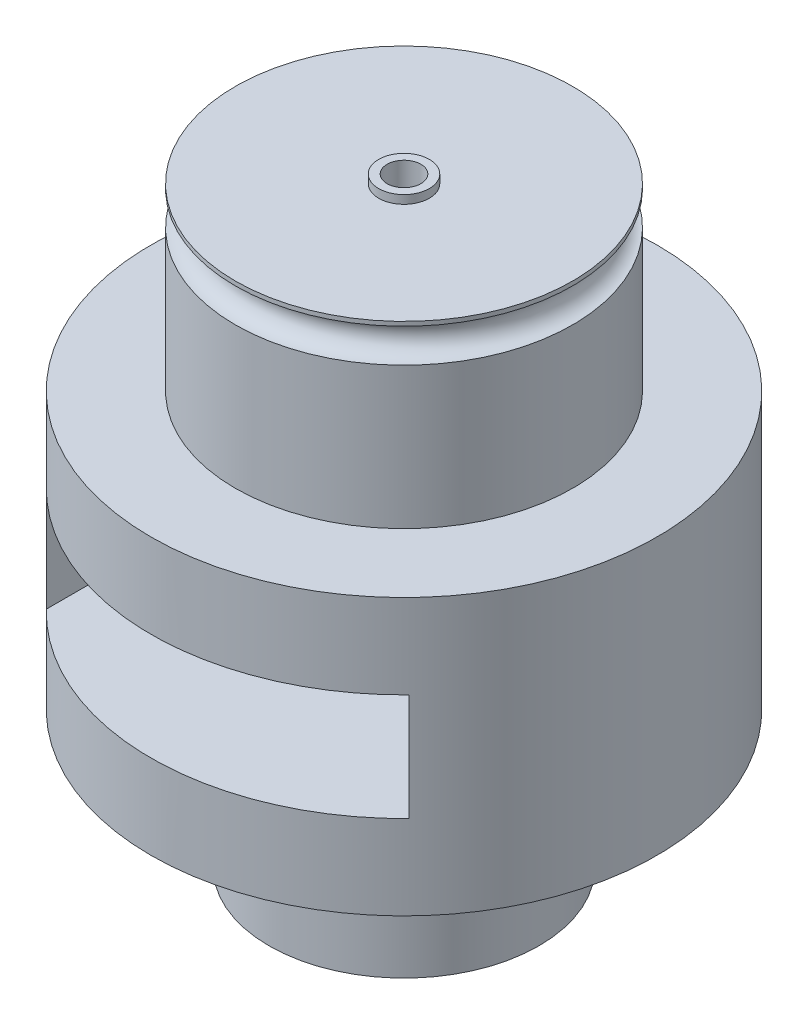
SolidWorks part; units mm, degrees
ref_plane "Front Plane" through (0, 0, 0) normal (0, 0, 1) x (1, 0, 0)
ref_plane "Top Plane" through (0, 0, 0) normal (0, 1, 0) x (1, 0, 0)
ref_plane "Right Plane" through (0, 0, 0) normal (1, 0, 0) x (0, 0, -1)
sketch "Sketch1" plane through (0, 0, 0) normal (0, 1, 0) x (1, 0, 0)
  circle A0 centre (0, 0) radius 15
  circle A1 centre (0, 0) radius 1
  dimension "D1" = 2
  dimension "D2" = 30
extrude "Boss-Extrude1" add sketch "Sketch1" along normal blind 32.6375 contours A0
sketch "Sketch2" plane through (0, 0, 0) normal (0, 0, 1) x (1, 0, 0)
  line L0 (0, 0) -> (0, 32.6375) construction
  line L1 (-10.75, 13.1438) -> (10.75, 13.1438)
  line L2 (-10.75, 13.1438) -> (-10.75, 19.4938)
  line L3 (-10.75, 19.4938) -> (10.75, 19.4938)
  line L4 (10.75, 13.1438) -> (10.75, 19.4938)
  line L5 (-10.75, 13.1438) -> (10.75, 19.4938) construction
  line L6 (-10.75, 19.4938) -> (10.75, 13.1438) construction
  line L9 (15, 32.6375) -> (-15, 32.6375) construction
  point P0 (0, 16.3188)
  point P11 (6.6425, 0)
  point P12 (0, 16.3188)
  dimension "D1" = 6.35
  dimension "D2" = 21.5
extrude "Cut-Extrude1" cut sketch "Sketch2" against normal through all both and the other way through all
sketch "Sketch3" plane through (0, 0, 0) normal (0, -1, 0) x (-1, 0, 0)
  circle A0 centre (0, 0) radius 1.5
  circle A1 centre (0, 0) radius 1
  dimension "D1" = 3
  dimension "D2" = 2
extrude "Boss-Extrude2" add sketch "Sketch3" along normal blind 0.5
sketch "Sketch4" plane through (0, 32.6375, 0) normal (0, 1, 0) x (1, 0, 0)
  circle A0 centre (0, 0) radius 10
  circle A1 centre (0, 0) radius 1
  dimension "D1" = 20
  dimension "D2" = 2
extrude "Boss-Extrude3" add sketch "Sketch4" along normal blind 2.5
ref_plane "Plane1" through (0, 33.8875, 0) normal (0, 1, 0) x (1, 0, 0)
sketch "Sketch77" plane through (0, 33.8875, 0) normal (0, 1, 0) x (1, 0, 0)
  circle A0 centre (0, 0) radius 10
  circle A1 centre (0, 0) radius 10
sweep "Cut-Sweep2" cut path "Sketch77" circular profile diameter 2 parameters "D3"=2
sketch "Sketch82" plane through (0, 35.1375, 0) normal (0, 1, 0) x (1, 0, 0)
  circle A0 centre (0, 0) radius 1
  circle A1 centre (0, 0) radius 1.5
  dimension "D1" = 3
  dimension "D2" = 2
extrude "Boss-Extrude5" add sketch "Sketch82" along normal blind 0.5
sketch "Sketch91" plane through (0, 0, 0) normal (0, -1, 0) x (1, 0, 0)
  circle A0 centre (0, 0) radius 15
  circle A1 centre (0, 0) radius 8
  circle A2 centre (0, 0) radius 6 construction
  circle A3 centre (0, 0) radius 15 construction
  dimension "D1" = 2
extrude "Cut-Extrude2" cut sketch "Sketch91" against normal offset from surface 5 and the other way through all up to face at (0, 13.1438, -1)
sketch "Sketch92" plane through (0, 32.6375, 0) normal (0, 1, 0) x (1, 0, 0)
  circle A0 centre (0, 0) radius 15
  circle A1 centre (0, 0) radius 10
  circle A3 centre (0, 0) radius 15 construction
  circle A4 centre (0, 0) radius 10 construction
extrude "Cut-Extrude3" cut sketch "Sketch92" against normal offset from surface (8.1437 mm away) 5 up to face at (0, 19.4938, 1)
